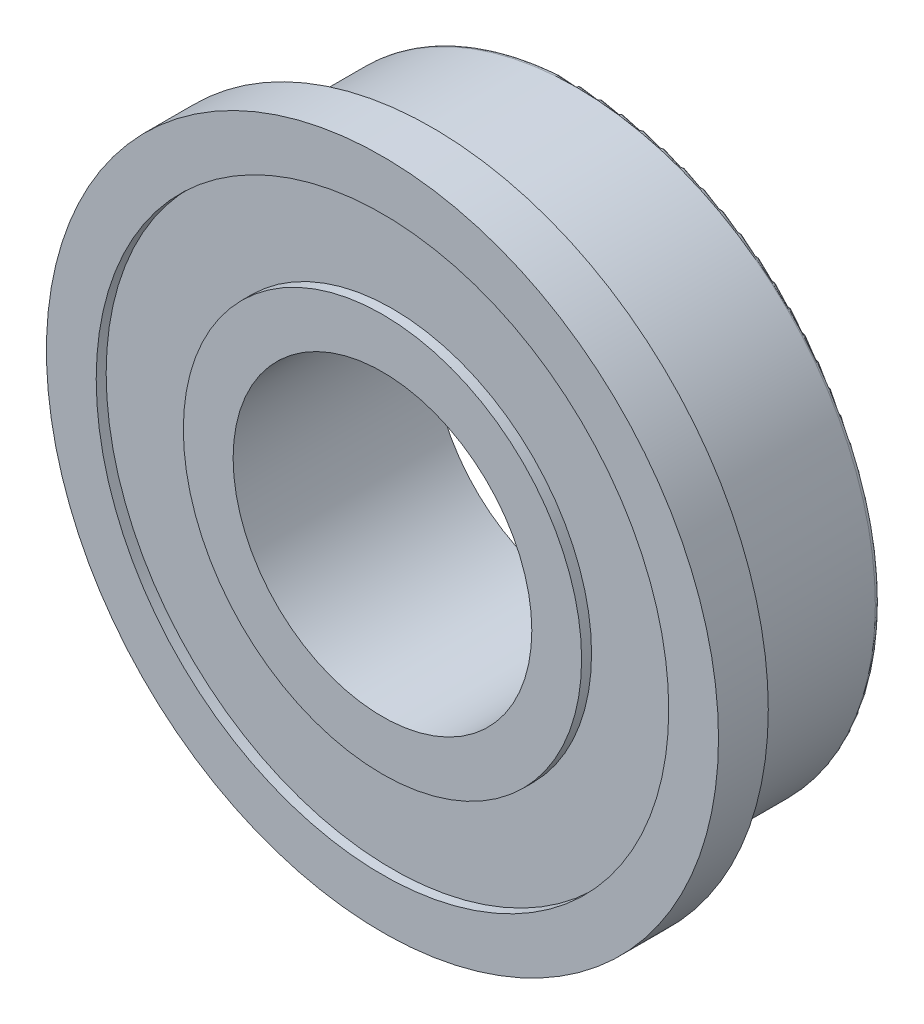
SolidWorks part; units mm, degrees
ref_plane "前基準面" through (0, 0, 0) normal (0, 0, 1) x (1, 0, 0)
ref_plane "上基準面" through (0, 0, 0) normal (0, 1, 0) x (1, 0, 0)
ref_plane "右基準面" through (0, 0, 0) normal (1, 0, 0) x (0, 0, -1)
sketch "草圖1" plane through (0, 0, 0) normal (0, 0, 1) x (1, 0, 0)
  circle A0 centre (0, 0) radius 6
  dimension "D1" = 12
extrude "填料-伸長1" add sketch "草圖1" along normal blind 4
sketch "草圖2" plane through (0, 0, 4) normal (0, 0, 1) x (1, 0, 0)
  circle A0 centre (0, 0) radius 6.75
  dimension "D1" = 13.5
extrude "填料-伸長2" add sketch "草圖2" against normal blind 1
sketch "草圖3" plane through (0, 0, 0) normal (0, 0, -1) x (-1, 0, 0)
  circle A0 centre (0, 0) radius 3
  dimension "D1" = 6
extrude "除料-伸長1" cut sketch "草圖3" against normal through all
sketch "草圖4" plane through (0, 0, 0) normal (0, 0, -1) x (-1, 0, 0)
  circle A0 centre (0, 0) radius 5
  circle A1 centre (0, 0) radius 4
  circle A2 centre (0, 0) radius 6 construction
  circle A3 centre (0, 0) radius 3 construction
  dimension "D1" = 1
  dimension "D2" = 1
extrude "除料-伸長2" cut sketch "草圖4" against normal blind 0.2
sketch "草圖5" plane through (0, 0, 4) normal (0, 0, 1) x (1, 0, 0)
  circle A0 centre (0, 0) radius 4
  circle A1 centre (0, 0) radius 5.75
  circle A2 centre (0, 0) radius 3 construction
  circle A4 centre (0, 0) radius 6.75 construction
  dimension "D1" = 1
  dimension "D2" = 1
extrude "除料-伸長3" cut sketch "草圖5" against normal blind 0.2
fillet "圓角1" radius 0.1 1 edges at (6, 0, 0)
